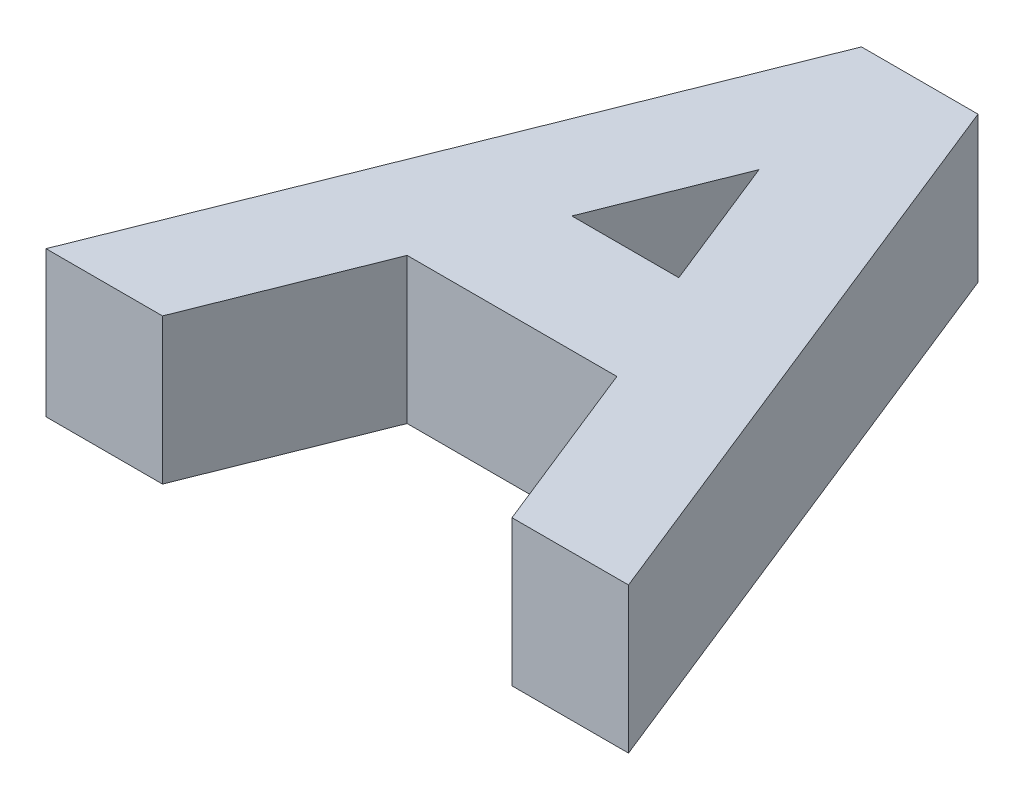
SolidWorks part; units mm, degrees
ref_plane "Front Plane" through (0, 0, 0) normal (0, 0, 1) x (1, 0, 0)
ref_plane "Top Plane" through (0, 0, 0) normal (0, 1, 0) x (1, 0, 0)
ref_plane "Right Plane" through (0, 0, 0) normal (1, 0, 0) x (0, 0, -1)
sketch "Sketch1" plane through (0, 0, 0) normal (0, 1, 0) x (1, 0, 0)
  line L0 (0, 0) -> (16, 40)
  line L1 (16, 40) -> (24, 40)
  line L2 (24, 40) -> (40, 0)
  line L3 (40, 0) -> (32, 0)
  line L4 (32, 0) -> (27.2, 12)
  line L5 (27.2, 12) -> (12.8, 12)
  line L6 (12.8, 12) -> (8, 0)
  line L7 (8, 0) -> (0, 0)
  line L8 (16.1106, 20) -> (19.7819, 29.1784)
  line L9 (19.7819, 29.1784) -> (23.4533, 20)
  line L10 (23.4533, 20) -> (16.1106, 20)
  dimension "D1" = 40
  dimension "D2" = 40
  dimension "D7" = 12
  dimension "D8" = 8
extrude "Boss-Extrude1" add sketch "Sketch1" along normal blind 10
